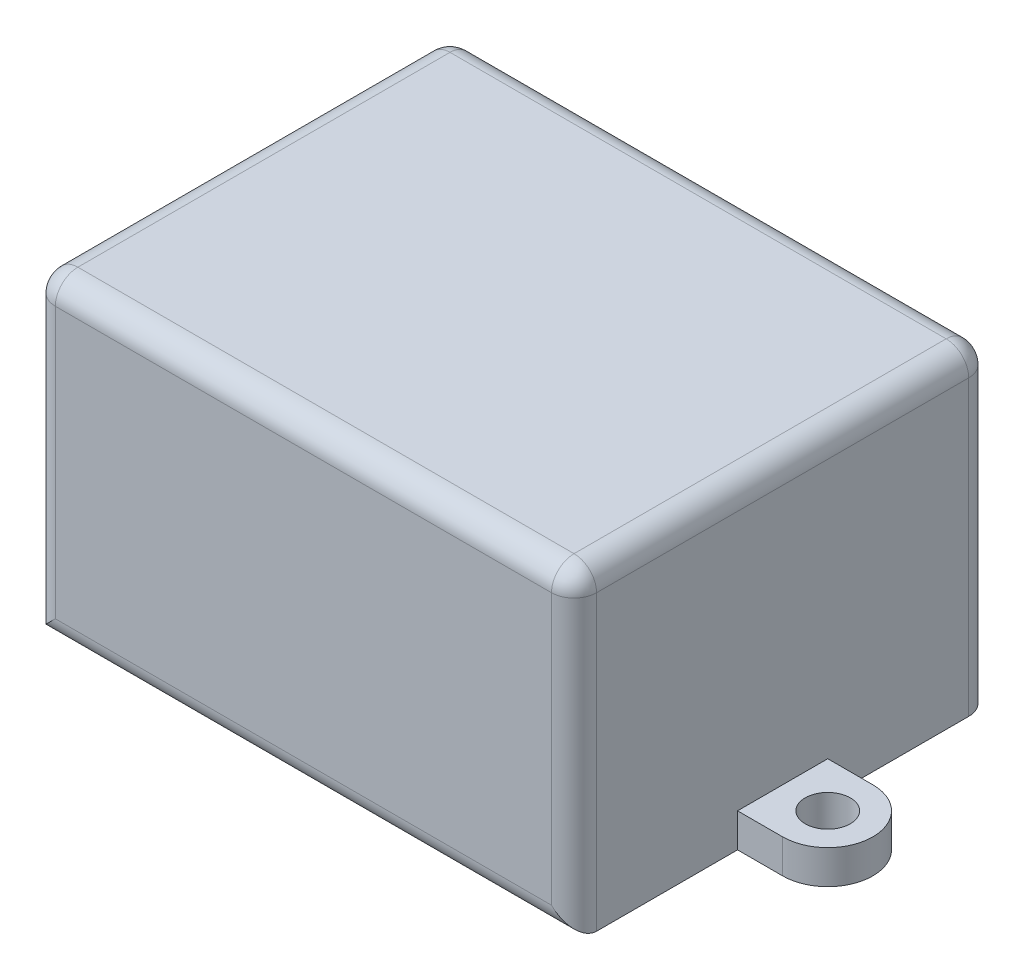
SolidWorks part; units mm, degrees
ref_plane "前视基准面" through (0, 0, 0) normal (0, 0, 1) x (1, 0, 0)
ref_plane "上视基准面" through (0, 0, 0) normal (0, 1, 0) x (1, 0, 0)
ref_plane "右视基准面" through (0, 0, 0) normal (1, 0, 0) x (0, 0, -1)
sketch "草图1" plane through (0, 0, 0) normal (0, 0, 1) x (1, 0, 0)
  line L1 (0, 0) -> (48, 0)
  line L2 (0, 0) -> (0, 28)
  line L3 (0, 28) -> (48, 28)
  line L4 (48, 0) -> (48, 28)
  dimension "D1" = 28
  dimension "D2" = 48
extrude "凸台-拉伸1" add sketch "草图1" along normal blind 37
fillet "圆角1" radius 2 9 edges at (48, 14, 37) (24, 0, 37) (0, 14, 37) (48, 28, 18.5) (24, 28, 37) (0, 28, 18.5) (24, 28, 0) (0, 14, 0) (48, 14, 0)
sketch "草图2" plane through (0, 0, 0) normal (0, -1, 0) x (1, 0, 0)
  line L0 (0, 18.5) -> (48, 18.5)
  line L1 (-4, 18.5) -> (52, 18.5) construction
  line L2 (-4, 22.5) -> (52, 22.5)
  line L3 (-4, 14.5) -> (52, 14.5)
  line L4 (48, 2) -> (48, 35)
  line L5 (48, 35) -> (0, 35)
  line L6 (0, 35) -> (0, 2)
  line L7 (2, 0) -> (46, 0)
  line L8 (48, 2) -> (48, 35)
  line L9 (48, 35) -> (0, 35)
  line L10 (0, 35) -> (0, 2)
  line L11 (2, 0) -> (46, 0)
  circle A0 centre (-4, 18.5) radius 2
  circle A1 centre (52, 18.5) radius 2
  arc A2 (0, 2) -> (2, 0) centre (2, 2) ccw
  arc A3 (46, 0) -> (48, 2) centre (46, 2) ccw
  arc A4 (0, 2) -> (2, 0) centre (2, 2) ccw
  arc A5 (46, 0) -> (48, 2) centre (46, 2) ccw
  arc A6 (-4, 22.5) -> (-4, 14.5) centre (-4, 18.5) ccw
  arc A7 (52, 14.5) -> (52, 22.5) centre (52, 18.5) ccw
  point P14 (24, 18.5)
  dimension "D4" = 4
  dimension "D5" = 4
  dimension "D6" = 4
  dimension "D2" = 4
  dimension "D3" = 4
  dimension "D7" = 56
  dimension "D1" = 0
extrude "凸台-拉伸2" add sketch "草图2" against normal blind 3
